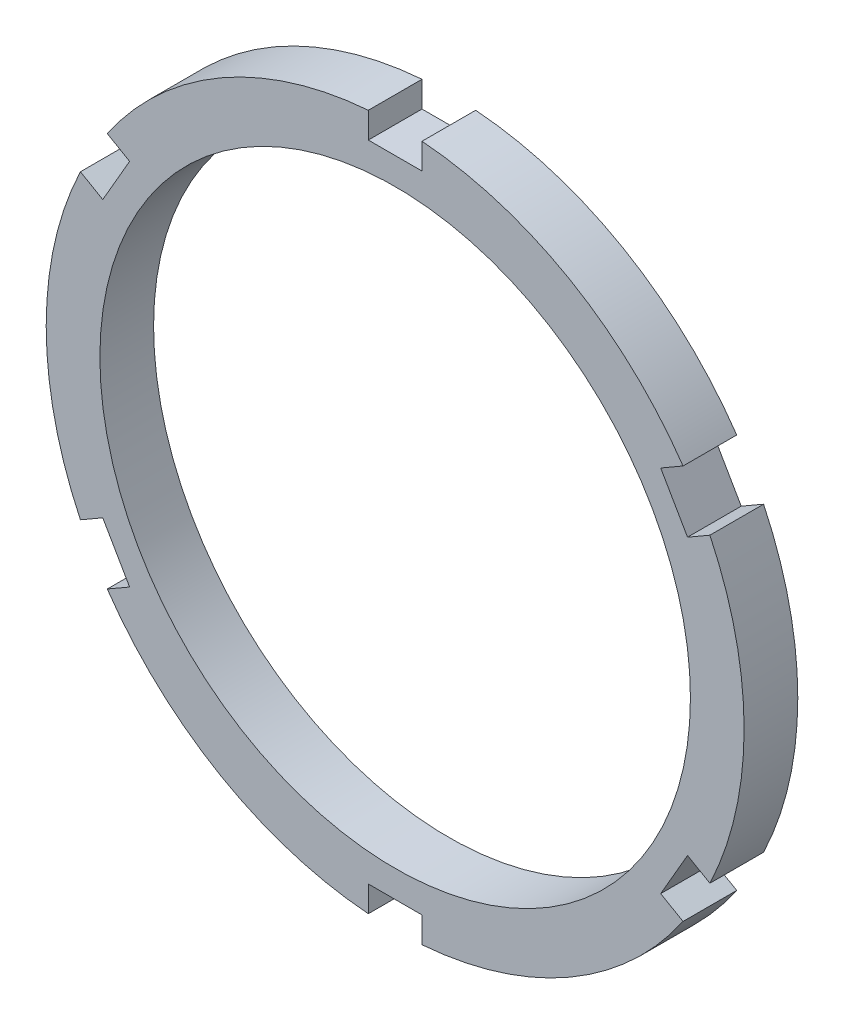
SolidWorks part; units mm, degrees
material "Balsa"
ref_plane "Alzado" through (0, 0, 0) normal (0, 0, 1) x (1, 0, 0)
ref_plane "Planta" through (0, 0, 0) normal (0, 1, 0) x (1, 0, 0)
ref_plane "Vista lateral" through (0, 0, 0) normal (1, 0, 0) x (0, 0, -1)
sketch "Sketch1" plane through (0, 0, 0) normal (0, 0, 1) x (1, 0, 0)
  circle A0 centre (0, 0) radius 65
  dimension "D1" = 130
extrude "Boss-Extrude1" add sketch "Sketch1" along normal blind 10
sketch "Sketch2" plane through (0, 0, 10) normal (0, 0, 1) x (1, 0, 0)
  circle A0 centre (0, 0) radius 55
  dimension "D1" = 110
extrude "Cut-Extrude1" cut sketch "Sketch2" against normal through all
sketch "Sketch3" plane through (0, 0, 10) normal (0, 0, 1) x (1, 0, 0)
  line L0 (0, 0) -> (0, 84.7774) construction
  line L5 (49.4615, 34.3301) -> (53.7917, 36.8301)
  line L6 (-5, 60) -> (5, 60)
  line L7 (-5, 60) -> (-5, 65)
  line L8 (-5, 65) -> (5, 65)
  line L9 (5, 60) -> (5, 65)
  line L10 (54.4615, 25.6699) -> (58.7917, 28.1699)
  line L11 (53.7917, 36.8301) -> (58.7917, 28.1699)
  line L12 (49.4615, 34.3301) -> (54.4615, 25.6699)
  line L13 (54.4615, -25.6699) -> (58.7917, -28.1699)
  line L14 (49.4615, -34.3301) -> (53.7917, -36.8301)
  line L15 (58.7917, -28.1699) -> (53.7917, -36.8301)
  line L16 (54.4615, -25.6699) -> (49.4615, -34.3301)
  line L17 (5, -60) -> (5, -65)
  line L18 (-5, -60) -> (-5, -65)
  line L19 (5, -65) -> (-5, -65)
  line L20 (5, -60) -> (-5, -60)
  line L21 (-49.4615, -34.3301) -> (-53.7917, -36.8301)
  line L22 (-54.4615, -25.6699) -> (-58.7917, -28.1699)
  line L23 (-53.7917, -36.8301) -> (-58.7917, -28.1699)
  line L24 (-49.4615, -34.3301) -> (-54.4615, -25.6699)
  line L25 (-54.4615, 25.6699) -> (-58.7917, 28.1699)
  line L26 (-49.4615, 34.3301) -> (-53.7917, 36.8301)
  line L27 (-58.7917, 28.1699) -> (-53.7917, 36.8301)
  line L28 (-54.4615, 25.6699) -> (-49.4615, 34.3301)
  point P22 (0, 0)
  point P28 (0, 0)
  dimension "D1" = 10
  dimension "D2" = 5
  dimension "D3" = 5
  dimension "D4" = 60
  dimension "D5" = 6
extrude "Cut-Extrude4" cut sketch "Sketch3" against normal through all
